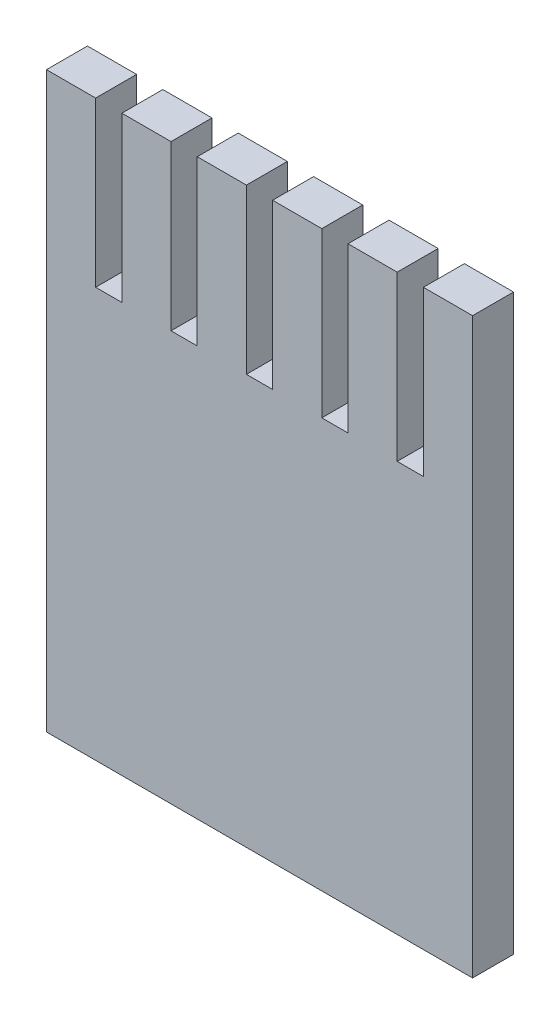
SolidWorks part; units mm, degrees
ref_plane "前视基准面" through (0, 0, 0) normal (0, 0, 1) x (1, 0, 0)
ref_plane "上视基准面" through (0, 0, 0) normal (0, 1, 0) x (1, 0, 0)
ref_plane "右视基准面" through (0, 0, 0) normal (1, 0, 0) x (0, 0, -1)
other "Configuration Table"
sketch "Sketch1" plane through (0, 0, 0) normal (0, 0, 1) x (1, 0, 0)
  line L0 (0, 25) -> (26, 25)
  line L1 (0, 0) -> (26, 0)
  line L2 (0, 0) -> (0, 35)
  line L3 (0, 35) -> (26, 35)
  line L4 (26, 0) -> (26, 35)
  line L5 (4.6, 35) -> (7.6, 35)
  line L6 (0, 35) -> (3, 35)
  line L7 (0, 35) -> (0, 25)
  line L8 (0, 25) -> (3, 25)
  line L9 (3, 35) -> (3, 25)
  line L10 (4.6, 35) -> (4.6, 25)
  line L11 (4.6, 25) -> (7.6, 25)
  line L12 (7.6, 35) -> (7.6, 25)
  line L13 (9.2, 35) -> (12.2, 35)
  line L14 (9.2, 35) -> (9.2, 25)
  line L15 (9.2, 25) -> (12.2, 25)
  line L16 (12.2, 35) -> (12.2, 25)
  line L17 (13.8, 35) -> (16.8, 35)
  line L18 (13.8, 35) -> (13.8, 25)
  line L19 (13.8, 25) -> (16.8, 25)
  line L20 (16.8, 35) -> (16.8, 25)
  line L21 (18.4, 35) -> (21.4, 35)
  line L22 (18.4, 35) -> (18.4, 25)
  line L23 (18.4, 25) -> (21.4, 25)
  line L24 (21.4, 35) -> (21.4, 25)
  line L25 (23, 35) -> (26, 35)
  line L26 (23, 35) -> (23, 25)
  line L27 (23, 25) -> (26, 25)
  line L28 (26, 35) -> (26, 25)
  dimension "D1" = 26
  dimension "D2" = 35
  dimension "D3" = 25
  dimension "D4" = 3
  dimension "D5" = 6
extrude "Boss-Extrude1" add sketch "Sketch1" along normal blind 2.5 contours L1 L4 L0 L2 | L9 L3 L2 L0 | L12 L3 L10 L0 | L16 L3 L14 L0 | L20 L3 L18 L0 | L24 L3 L22 L0 | L3 L26 L0 L4
